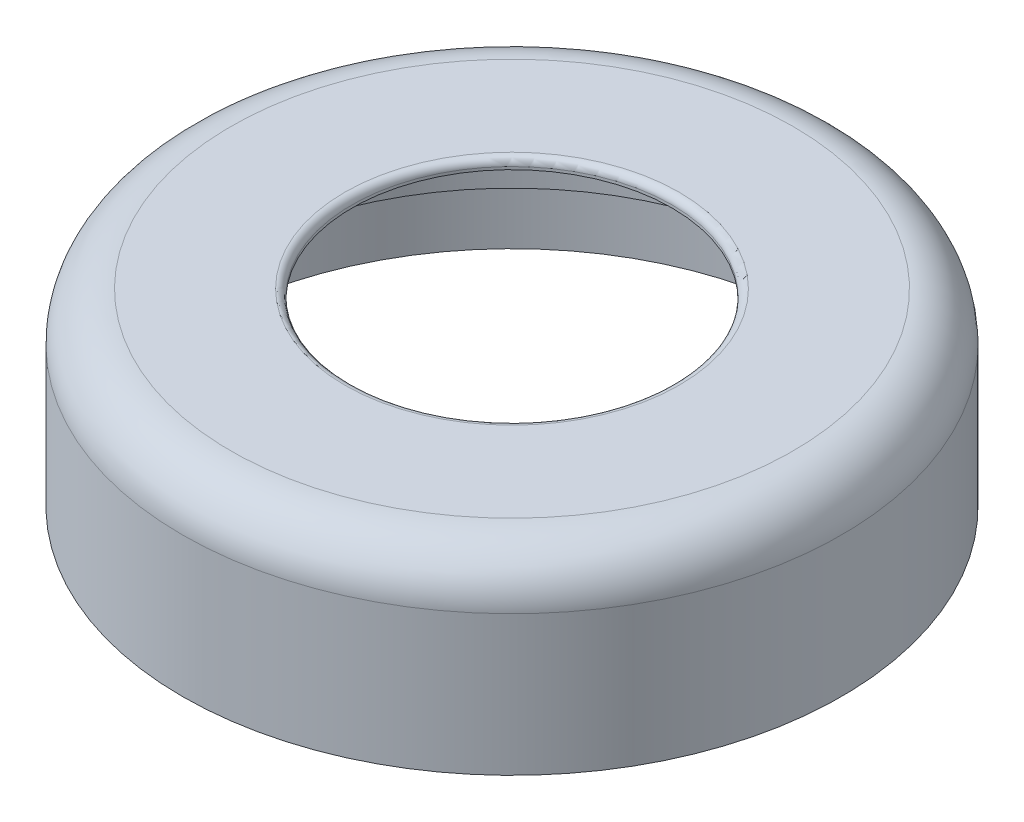
SolidWorks part; units mm, degrees
ref_plane "Front Plane" through (0, 0, 0) normal (0, 0, 1) x (1, 0, 0)
ref_plane "Top Plane" through (0, 0, 0) normal (0, 1, 0) x (1, 0, 0)
ref_plane "Right Plane" through (0, 0, 0) normal (1, 0, 0) x (0, 0, -1)
sketch "Sketch5" plane through (0, 0, 0) normal (0, 0, 1) x (1, 0, 0)
  line L1 (30.3, 7.697) -> (30.3, 16.1102)
  line L12 (16.4981, 20.1384) -> (29, 20.1384)
  line L13 (0, 0) -> (0, 20.1384) construction
  line L15 (16.4981, 19.1102) -> (22.4981, 19.1102)
  line L17 (16.4981, 20.1384) -> (16.4981, 19.1102)
  line L24 (34, 15.1384) -> (34, 0.697)
  line L33 (27.3, 19.1102) -> (22.4981, 19.1102)
  line L39 (32.55, 7.697) -> (32.55, 0.697)
  line L40 (32.55, 0.697) -> (34, 0.697)
  line L42 (30.3, 7.697) -> (32.55, 7.697)
  arc A0 (34, 15.1384) -> (29, 20.1384) centre (29, 15.1384) ccw
  arc A1 (30.3, 16.1102) -> (27.3, 19.1102) centre (27.3, 16.1102) ccw
  point P7 (0, 0)
  point P10 (0, 0)
  dimension "D1" = 5
  dimension "D2" = 32.55
  dimension "D4" = 3
  dimension "D3" = 1.45
  dimension "D5" = 2.25
  dimension "D6" = 7
  dimension "D7" = 14.4414
revolve "Revolve1" add sketch "Sketch5" angle 360 about L13
fillet "Fillet2" radius 0.75 1 edges at (0, 20.1384, -16.4981)
sketch "Sketch8" plane through (0, 0.697, 0) normal (0, -1, 0) x (1, 0, 0)
  line L0 (0, 0) -> (0, -32.55) construction
  line L1 (-5, -30.1637) -> (5, -30.1637)
  line L2 (-5, -30.1637) -> (-5, -32.1637)
  line L3 (5, -30.1637) -> (5, -32.1637)
  line L4 (-28.6225, 10.7517) -> (-30.3546, 11.7517)
  line L5 (-23.6225, 19.412) -> (-28.6225, 10.7517)
  line L6 (-23.6225, 19.412) -> (-25.3546, 20.412)
  line L7 (23.6225, 19.412) -> (25.3546, 20.412)
  line L8 (28.6225, 10.7517) -> (23.6225, 19.412)
  line L9 (28.6225, 10.7517) -> (30.3546, 11.7517)
  circle A0 centre (0, 0) radius 32.55 construction
  circle A2 centre (0, 0) radius 32.55 construction
  arc A3 (-5, -32.1637) -> (5, -32.1637) centre (0, 0) ccw
  arc A4 (-25.3546, 20.412) -> (-30.3546, 11.7517) centre (0, 0) ccw
  arc A5 (30.3546, 11.7517) -> (25.3546, 20.412) centre (0, 0) ccw
  point P9 (0, -30.1637)
  dimension "D1" = 3
  dimension "D2" = 2
extrude "Boss-Extrude4" add sketch "Sketch8" against normal up to surface (7 mm away) up to face at (0, 7.697, -32.55)
